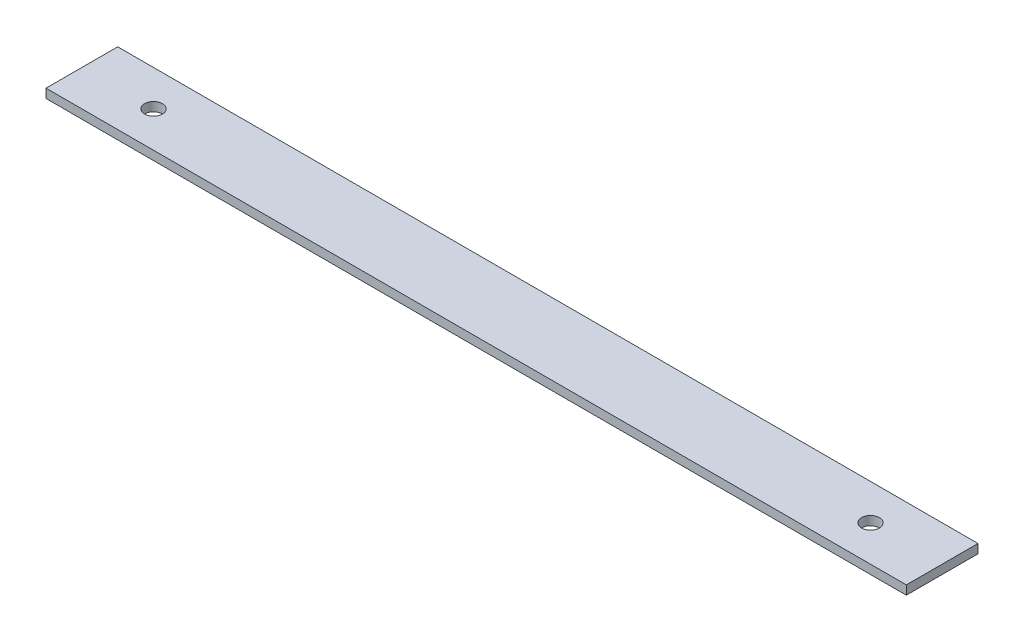
SolidWorks part; units mm, degrees
ref_plane "Front" through (0, 0, 0) normal (0, 0, 1) x (1, 0, 0)
ref_plane "Top" through (0, 0, 0) normal (0, 1, 0) x (1, 0, 0)
ref_plane "Right" through (0, 0, 0) normal (1, 0, 0) x (0, 0, -1)
sketch "Sketch1" plane through (0, 0, 0) normal (0, 1, 0) x (1, 0, 0)
  line L1 (0, 0) -> (304.8, 0)
  line L2 (0, 0) -> (0, 25.4)
  line L3 (0, 25.4) -> (304.8, 25.4)
  line L4 (304.8, 0) -> (304.8, 25.4)
  line L5 (0, 0) -> (304.8, 25.4) construction
  line L6 (0, 25.4) -> (304.8, 0) construction
  point P4 (152.4, 12.7)
  dimension "D1" = 25.4
  dimension "D2" = 304.8
extrude "Boss-Extrude1" add sketch "Sketch1" along normal blind 3.175
sketch "Sketch2" plane through (0, 3.175, 0) normal (0, 1, 0) x (1, 0, 0)
  line L0 (304.8, 0) -> (304.8, 25.4) construction
  line L1 (0, 25.4) -> (0, 0) construction
  line L3 (0, 12.7) -> (25.4, 12.7) construction
  line L4 (304.8, 12.7) -> (279.4, 12.7) construction
  circle A0 centre (279.4, 12.7) radius 3.175
  circle A2 centre (25.4, 12.7) radius 3.175
  dimension "D1" = 6.35
  dimension "D5" = 6.35
  dimension "D6" = 25.4
  dimension "D2" = 25.4
extrude "Cut-Extrude1" cut sketch "Sketch2" against normal through all
